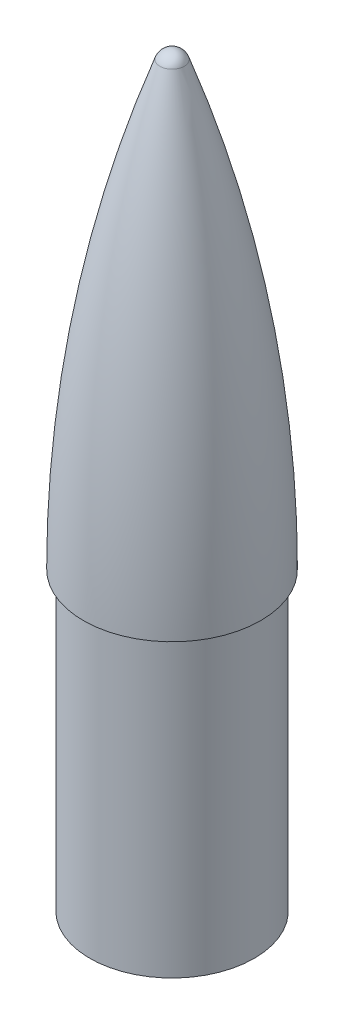
SolidWorks part; units mm, degrees
material "PLA"
ref_plane "Front Plane" through (0, 0, 0) normal (0, 0, 1) x (1, 0, 0)
ref_plane "Top Plane" through (0, 0, 0) normal (0, 1, 0) x (1, 0, 0)
ref_plane "Right Plane" through (0, 0, 0) normal (1, 0, 0) x (0, 0, -1)
sketch "Sketch1" plane through (0, 0, 0) normal (0, 0, 1) x (1, 0, 0)
  line L0 (-20.555, 0) -> (-20.555, -8.881) construction
  line L1 (-19.055, 0) -> (-20.555, 0)
  line L2 (0, 102.3969) -> (0, 104.3969)
  line L3 (0, 110) -> (-20.555, 110) construction
  line L4 (-20.555, 0) -> (-20.555, 110) construction
  line L6 (0, 0) -> (0, -68.5545) construction
  line L7 (-17.055, -68.5545) -> (-19.055, -68.5545)
  line L8 (-19.055, 0) -> (-19.055, -68.5545)
  line L9 (-17.055, 2) -> (-17.055, -68.5545) construction
  line L10 (-17.055, 2) -> (-18.5484, 2) construction
  line L11 (0, -68.5545) -> (-17.055, -68.5545) construction
  line L12 (0, 0) -> (0, 102.3969) construction
  line L13 (-10, 71.4455) -> (-10, -68.5545)
  line L14 (-17.055, -68.5545) -> (-10, -68.5545)
  line L15 (-10, 71.4455) -> (0, 71.4455)
  line L16 (0, 71.4455) -> (0, 102.3969)
  arc A0 (-20.555, 0) -> (-2.8254, 102.4055) centre (284.0548, 0) cw
  arc A1 (0, 104.3969) -> (-2.8254, 102.4055) centre (0, 101.3969) ccw
  arc A2 (-10, 71.4455) -> (-0.9418, 101.7331) centre (284.0548, 0) cw construction
  arc A3 (0, 102.3969) -> (-0.9418, 101.7331) centre (0, 101.3969) ccw construction
  arc A4 (-20.555, 0) -> (61.9638, 208.4772) centre (284.0548, 0) cw
  arc A5 (-18.5484, 2) -> (-10, 71.4455) centre (284.0548, 0) cw construction
  arc A6 (-18.5484, 2) -> (-0.9418, 101.7331) centre (284.0548, 0) cw construction
  dimension "D5" = 6
  dimension "D1" = 110
  dimension "D2" = 20.555
  dimension "D4" = 1.5
  dimension "D7" = 10
  dimension "D8" = 140
  dimension "D6" = 2
revolve "Revolve3" add sketch "Sketch1" angle 360 about L2
sketch "Sketch2" plane through (0, -68.5545, 0) normal (0, -1, 0) x (1, 0, 0)
  circle A0 centre (0, -14.055) radius 2.35
  circle A2 centre (0, 14.055) radius 2.35
  point P7 (0, 0)
  dimension "D1" = 4.7
  dimension "D3" = 2
  dimension "D2" = 14.055
extrude "Cut-Extrude1" cut sketch "Sketch2" against normal blind 10
